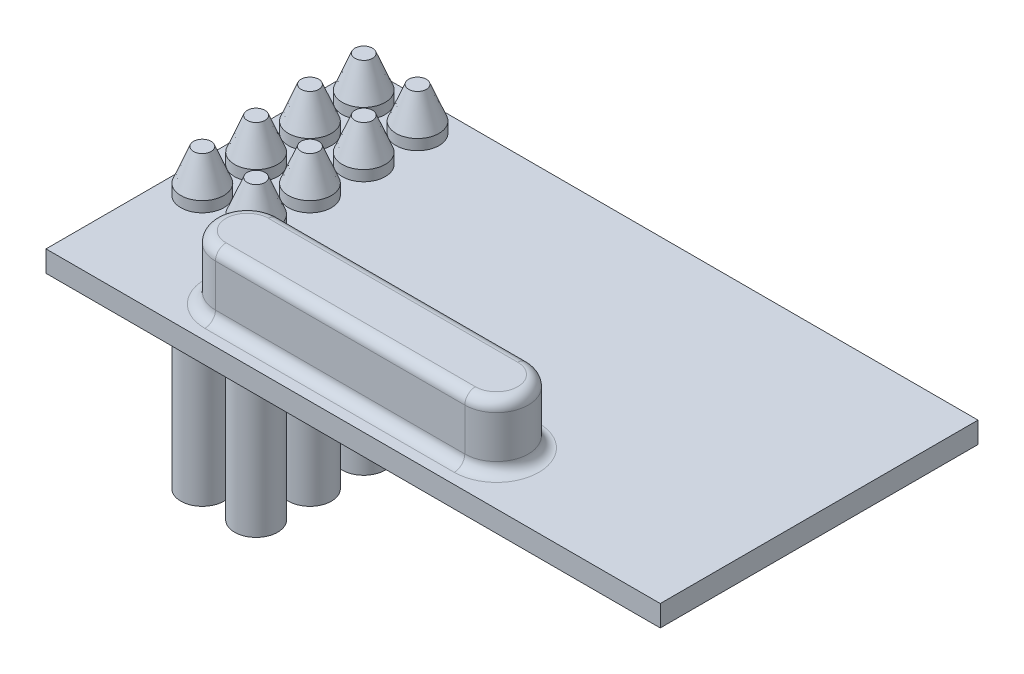
SolidWorks part; units mm, degrees
ref_plane "Plan de face" through (0, 0, 0) normal (0, 0, 1) x (1, 0, 0)
ref_plane "Plan de dessus" through (0, 0, 0) normal (0, 1, 0) x (1, 0, 0)
ref_plane "Plan de droite" through (0, 0, 0) normal (1, 0, 0) x (0, 0, -1)
sketch "Esquisse1" plane through (0, 0, 0) normal (0, 1, 0) x (1, 0, 0)
  line L1 (0, 0) -> (29, 0)
  line L2 (0, 0) -> (0, 15)
  line L3 (0, 15) -> (29, 15)
  line L4 (29, 0) -> (29, 15)
  dimension "D1" = 29
  dimension "D2" = 15
extrude "Boss.-Extru.1" add sketch "Esquisse1" along normal blind 1
sketch "Esquisse2" plane through (0, 1, 0) normal (0, 1, 0) x (1, 0, 0)
  line L0 (0, 15) -> (0, 0) construction
  line L1 (29, 15) -> (0, 15) construction
  circle A0 centre (1.5, 13.5) radius 1.016
  circle A1 centre (1.5, 10.96) radius 1.016
  circle A2 centre (1.5, 8.42) radius 1.016
  circle A3 centre (1.5, 5.88) radius 1.016
  circle A4 centre (4.04, 10.96) radius 1.016
  circle A5 centre (4.04, 8.42) radius 1.016
  circle A6 centre (4.04, 5.88) radius 1.016
  circle A7 centre (4.04, 13.5) radius 1.016
  dimension "D1" = 2.032
  dimension "D2" = 1.5
  dimension "D3" = 1.5
  dimension "D4" = 4
  dimension "D5" = 2
extrude "Boss.-Extru.2" add sketch "Esquisse2" along normal blind 2 and the other way blind 12
chamfer "Chanfrein1" distance 1.5 distance2 0.6 8 edges at (1.5, 3, -4.864) (1.5, 3, -7.404) (4.04, 3, -4.864) (4.04, 3, -7.404) (4.04, 3, -9.944) (1.5, 3, -9.944) (4.04, 3, -12.484) (1.5, 3, -12.484)
sketch "Esquisse3" plane through (0, 1, 0) normal (0, 1, 0) x (1, 0, 0)
  line L0 (7, 2.5) -> (18.7711, 2.5) construction
  line L1 (7, 4) -> (18.7711, 4)
  line L2 (7, 1) -> (18.7711, 1)
  line L3 (0, 0) -> (29, 0) construction
  line L4 (0, 15) -> (0, 0) construction
  arc A0 (7, 4) -> (7, 1) centre (7, 2.5) ccw
  arc A1 (18.7711, 1) -> (18.7711, 4) centre (18.7711, 2.5) ccw
  point P2 (12.8856, 2.5)
  dimension "D1" = 2.5
  dimension "D2" = 7
extrude "Boss.-Extru.3" add sketch "Esquisse3" along normal blind 3
fillet "Congé2" radius 0.5 4 edges at (12.8856, 4, -4) (20.2711, 4, -2.5) (12.8856, 4, -1) (5.5, 4, -2.5)
fillet "Congé3" radius 0.5 4 edges at (12.8856, 1, -4) (20.2711, 1, -2.5) (12.8856, 1, -1) (5.5, 1, -2.5)
